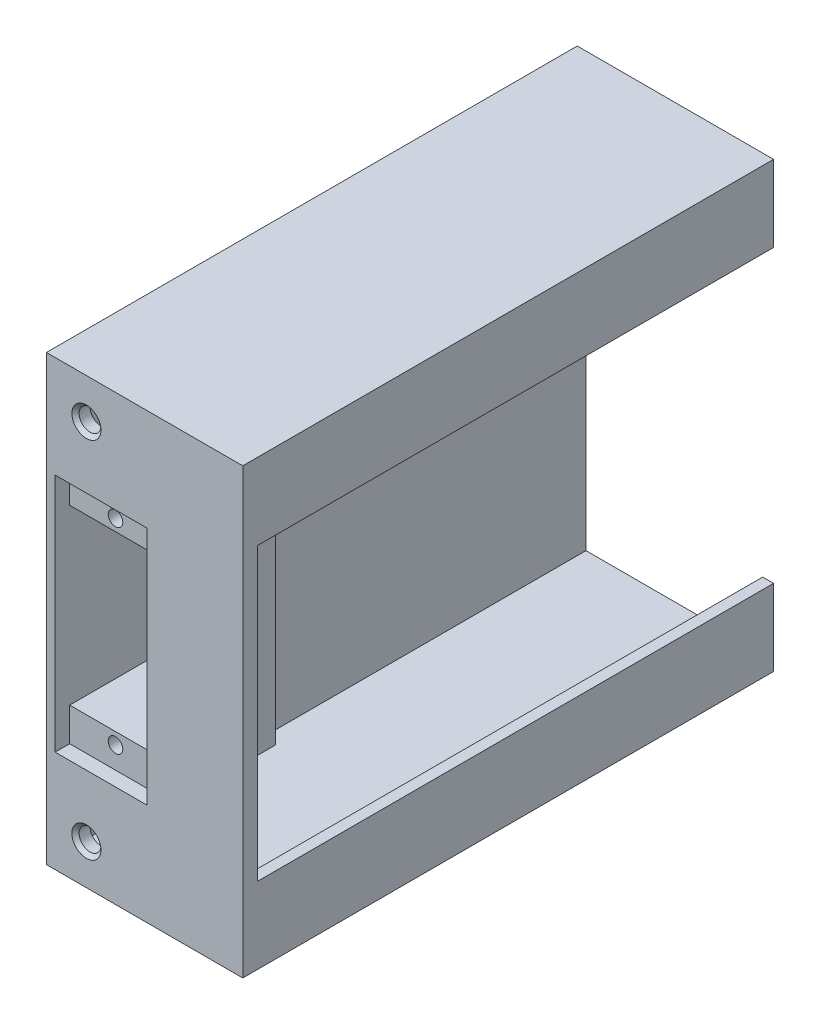
SolidWorks part; units mm, degrees
ref_plane "前视基准面" through (0, 0, 0) normal (0, 0, 1) x (1, 0, 0)
ref_plane "上视基准面" through (0, 0, 0) normal (0, 1, 0) x (1, 0, 0)
ref_plane "右视基准面" through (0, 0, 0) normal (1, 0, 0) x (0, 0, -1)
other "Configuration Table"
sketch "草图1" plane through (0, 0, 0) normal (1, 0, 0) x (0, 0, -1)
  line L1 (36.5, -30.5) -> (-36.5, -30.5)
  line L2 (36.5, -30.5) -> (36.5, 30.5)
  line L3 (36.5, 30.5) -> (-36.5, 30.5)
  line L4 (-36.5, -30.5) -> (-36.5, 30.5)
  line L5 (36.5, -30.5) -> (-36.5, 30.5) construction
  line L6 (36.5, 30.5) -> (-36.5, -30.5) construction
  point P0 (0, 0)
  dimension "D1" = 61
  dimension "D2" = 73
extrude "凸台-拉伸1" add sketch "草图1" against normal blind 1.5
sketch "草图3" plane through (0, 0, 0) normal (1, 0, 0) x (0, 0, -1)
  line L0 (-36.5, 30.5) -> (-36.5, -30.5) construction
  line L1 (36.5, 30.5) -> (-36.5, 30.5)
  line L2 (36.5, 30.5) -> (36.5, 29)
  line L3 (36.5, 29) -> (-36.5, 29)
  line L4 (-36.5, 30.5) -> (-36.5, 29)
  line L6 (36.5, -30.5) -> (-36.5, -30.5)
  line L7 (36.5, -30.5) -> (36.5, -29)
  line L8 (36.5, -29) -> (-36.5, -29)
  line L9 (-36.5, -30.5) -> (-36.5, -29)
  dimension "D1" = 1.5
  dimension "D2" = 1.5
extrude "凸台-拉伸2" add sketch "草图3" along normal blind 24
sketch "草图4" plane through (0, 0, 36.5) normal (0, 0, 1) x (1, 0, 0)
  line L1 (0, 29) -> (24, 29)
  line L2 (0, 29) -> (0, -29)
  line L3 (0, -29) -> (24, -29)
  line L4 (24, 29) -> (24, -29)
extrude "凸台-拉伸8" add sketch "草图4" against normal blind 2
sketch "草图18" plane through (0, 0, 34.5) normal (0, 0, -1) x (-1, 0, 0)
  line L0 (0, 0) -> (-43.1615, 0) construction
  line L1 (0, 29) -> (0, -29) construction
  line L2 (0, 11.5) -> (-12, 11.5)
  line L3 (0, 11.5) -> (0, -11.5)
  line L4 (0, -11.5) -> (-12, -11.5)
  line L5 (-12, 11.5) -> (-12, -11.5)
  point P9 (-12, 0)
  dimension "D1" = 12
  dimension "D2" = 23
extrude "切除-拉伸10" cut sketch "草图18" against normal blind 2
sketch "草图19" plane through (0, 0, 34.5) normal (0, 0, -1) x (-1, 0, 0)
  line L1 (0, 11.5) -> (-12, 11.5)
  line L2 (0, 11.5) -> (0, 17.5)
  line L3 (0, 17.5) -> (-12, 17.5)
  line L4 (-12, 11.5) -> (-12, 17.5)
  line L5 (0, -11.5) -> (-12, -11.5)
  line L6 (0, -11.5) -> (0, -17.5)
  line L7 (0, -17.5) -> (-12, -17.5)
  line L8 (-12, -11.5) -> (-12, -17.5)
  dimension "D1" = 6
  dimension "D2" = 6
extrude "凸台-拉伸9" add sketch "草图19" along normal blind 15
sketch "草图21" plane through (0, 0, 34.5) normal (0, 0, -1) x (-1, 0, 0)
  line L1 (-12, 17.5) -> (-13, 17.5)
  line L2 (-12, 17.5) -> (-12, -17.5)
  line L3 (-12, -17.5) -> (-13, -17.5)
  line L4 (-13, 17.5) -> (-13, -17.5)
  dimension "D1" = 1
extrude "凸台-拉伸10" add sketch "草图21" along normal blind 15
sketch "草图24" plane through (0, 0, 36.5) normal (0, 0, 1) x (1, 0, 0)
  line L1 (0, 11.5) -> (12, 11.5)
  line L2 (0, 11.5) -> (0, 16.5)
  line L3 (0, 16.5) -> (12, 16.5)
  line L4 (12, 11.5) -> (12, 16.5)
  line L5 (12, -11.5) -> (0, -11.5)
  line L6 (12, -11.5) -> (12, -16.5)
  line L7 (12, -16.5) -> (0, -16.5)
  line L8 (0, -11.5) -> (0, -16.5)
  dimension "D1" = 5
  dimension "D2" = 5
extrude "切除-拉伸12" cut sketch "草图24" against normal blind 2
sketch "草图25" plane through (0, 0, 34.5) normal (0, 0, 1) x (1, 0, 0)
  line L0 (6, 11.5) -> (6, -19.983) construction
  line L1 (0, 11.5) -> (12, 11.5) construction
  line L2 (12, -11.5) -> (0, -11.5) construction
  circle A0 centre (6, 13.5) radius 1
  circle A1 centre (6, -13.5) radius 1
  dimension "D3" = 2
  dimension "D4" = 2
  dimension "D1" = 2
  dimension "D2" = 2
extrude "切除-拉伸13" cut sketch "草图25" against normal blind 10
sketch "草图28" plane through (24, 0, 0) normal (1, 0, 0) x (0, 0, -1)
  line L0 (36.5, -29) -> (36.5, 29) construction
  line L1 (-36.5, 30.5) -> (36.5, 30.5)
  line L2 (-36.5, 30.5) -> (-36.5, 20)
  line L3 (-36.5, 20) -> (36.5, 20)
  line L4 (36.5, 30.5) -> (36.5, 20)
  line L6 (-36.5, -30.5) -> (36.5, -30.5)
  line L7 (-36.5, -30.5) -> (-36.5, -20)
  line L8 (-36.5, -20) -> (36.5, -20)
  line L9 (36.5, -30.5) -> (36.5, -20)
  dimension "D1" = 10.5
  dimension "D2" = 10.5
extrude "凸台-拉伸11" add sketch "草图28" along normal blind 1.5
sketch "草图31" plane through (24, 0, 0) normal (1, 0, 0) x (0, 0, -1)
  line L4 (-36.5, -20) -> (-34.5, -20)
  line L5 (-34.5, -20) -> (-34.5, 20)
  line L6 (-34.5, 20) -> (-36.5, 20)
  line L7 (-36.5, 20) -> (-36.5, -20)
  line L8 (-36.5, -20) -> (-34.5, -20)
  line L9 (-34.5, -20) -> (-34.5, 20)
  line L10 (-34.5, 20) -> (-36.5, 20)
  line L11 (-36.5, 20) -> (-36.5, -20)
  dimension "D1" = 0
extrude "凸台-拉伸12" add sketch "草图31" along normal up to surface (1.5 mm away) up to face at (25.5, 25.25, 0)
sketch "草图32" plane through (0, 0, 34.5) normal (0, 0, -1) x (-1, 0, 0)
  line L0 (-24, 29) -> (0, 29) construction
  line L2 (0, -29) -> (-24, -29) construction
  line L5 (0, -29) -> (0, 29) construction
  line L6 (0, -17.5) -> (0, -29) construction
  circle A0 centre (-4, 25) radius 1.5
  circle A1 centre (-4, -25) radius 1.5
  dimension "D5" = 3
  dimension "D6" = 3
  dimension "D1" = 4
  dimension "D2" = 4
  dimension "D3" = 4
  dimension "D4" = 4
extrude "切除-拉伸14" cut sketch "草图32" against normal blind 5
chamfer "倒角1" distance 0.5 angle 45 1 edges at (5.5, 25, 36.5)
chamfer "倒角2" distance 0.5 angle 45 1 edges at (5.5, -25, 36.5)
sketch "草图33" plane through (0, 0, 19.5) normal (0, 0, -1) x (-1, 0, 0)
  line L0 (0, -11.5) -> (-12, -11.5) construction
  line L1 (-12, -11.5) -> (-12, 11.5) construction
  line L2 (-12, 11.5) -> (0, 11.5) construction
  line L3 (0, -11.5) -> (-12, -11.5)
  line L4 (-12, -11.5) -> (-12, 11.5)
  line L5 (-12, 11.5) -> (0, 11.5)
  line L7 (0, 11.5) -> (0, 17.5) construction
  line L8 (0, 11.9) -> (-12.3, 11.9)
  line L9 (-12.3, 11.9) -> (-12.3, -11.9)
  line L10 (-12.3, -11.9) -> (0, -11.9)
  line L11 (0, -17.5) -> (0, -11.5) construction
  line L13 (0, 11.9) -> (0.3, 11.9)
  line L14 (0.3, 11.9) -> (0.3, -11.9)
  line L15 (0.3, -11.9) -> (0, -11.9)
  line L18 (0, 11.5) -> (0, -11.5)
  dimension "D1" = 0.4
  dimension "D2" = 0.4
  dimension "D3" = 0.3
  dimension "D4" = 0.3
extrude "切除-拉伸15" cut sketch "草图33" against normal blind 48
sketch "草图34" plane through (0, 0, -36.5) normal (0, 0, -1) x (-1, 0, 0)
  line L0 (0, -29) -> (0, 29) construction
  line L1 (0, -29) -> (0, 29)
  line L2 (0, 29) -> (0.3, 29)
  line L3 (0.3, 29) -> (0.3, -29)
  line L4 (0.3, -29) -> (0, -29)
  dimension "D1" = 0.3
extrude "切除-拉伸16" cut sketch "草图34" against normal up to surface (56 mm away) up to face at (6.325, 0, 19.5)
sketch "草图35" plane through (0, 0, 19.5) normal (0, 0, -1) x (-1, 0, 0)
  line L0 (0, 29) -> (0, 17.5) construction
  line L1 (0, 29) -> (0, 17.5)
  line L2 (0, 29) -> (0.3, 29)
  line L3 (0.3, 29) -> (0.3, 17.5)
  line L4 (0.3, -29) -> (0.3, 29) construction
  line L5 (0.3, 17.5) -> (0, 17.5)
  line L6 (0, -17.5) -> (0, -29)
  line L7 (0, -29) -> (0.3, -29)
  line L8 (0.3, -29) -> (0.3, -17.5)
  line L9 (0.3, -17.5) -> (0, -17.5)
extrude "切除-拉伸17" cut sketch "草图35" against normal up to surface (15 mm away) up to face at (2.5, 25, 34.5)
sketch "草图36" plane through (0, 0, 36.5) normal (0, 0, 1) x (1, 0, 0)
  line L0 (-0.3, -16.5) -> (12.3, -16.5)
  line L1 (12.3, -16.5) -> (12.3, -11.9)
  line L2 (12.3, -11.9) -> (-0.3, -11.9)
  line L3 (-0.3, -11.9) -> (-0.3, -16.5)
  line L4 (12.3, 11.9) -> (12.3, 16.5)
  line L5 (12.3, 16.5) -> (-0.3, 16.5)
  line L6 (-0.3, 16.5) -> (-0.3, 11.9)
  line L7 (-0.3, 11.9) -> (12.3, 11.9)
extrude "切除-拉伸18" cut sketch "草图36" against normal up to surface (2 mm away) up to face at (7, 13.5, 34.5)
